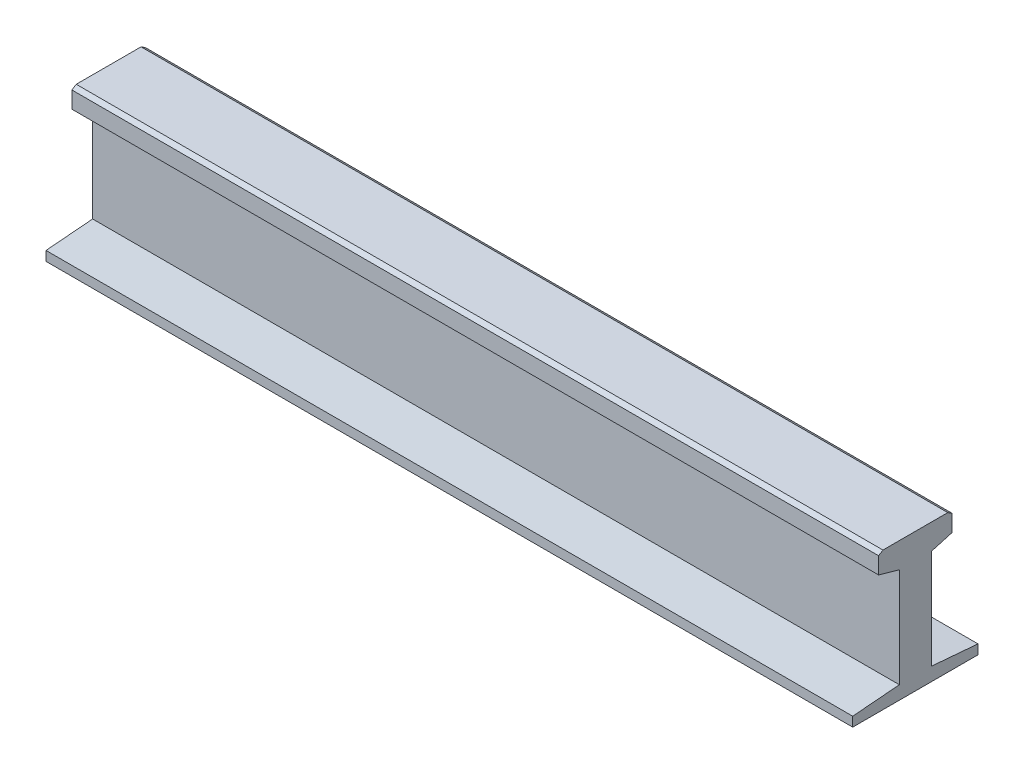
SolidWorks part; units mm, degrees
ref_plane "Спереди" through (0, 0, 0) normal (0, 0, 1) x (1, 0, 0)
ref_plane "Сверху" through (0, 0, 0) normal (0, 1, 0) x (1, 0, 0)
ref_plane "Справа" through (0, 0, 0) normal (1, 0, 0) x (0, 0, -1)
sketch "Эскиз1" plane through (0, 0, 0) normal (1, 0, 0) x (0, 0, -1)
  line L0 (-66, 0) -> (66, 0)
  line L1 (66, 0) -> (66, 10)
  line L2 (66, 10) -> (16.8833, 14.1635)
  line L3 (16.8833, 14.1635) -> (16.8833, 118.9844)
  line L4 (16.8833, 118.9844) -> (38.7045, 125.2191)
  line L5 (-34.151, 145.7096) -> (34.151, 145.7096)
  line L6 (34.151, 145.7096) -> (38.7045, 142.7824)
  line L7 (38.7045, 142.7824) -> (38.7045, 125.2191)
  line L8 (0, 177.3831) -> (0, -45.0863) construction
  line L9 (-38.7045, 142.7824) -> (-38.7045, 125.2191)
  line L10 (-34.151, 145.7096) -> (-38.7045, 142.7824)
  line L11 (-16.8833, 118.9844) -> (-38.7045, 125.2191)
  line L12 (-16.8833, 14.1635) -> (-16.8833, 118.9844)
  line L13 (-66, 10) -> (-16.8833, 14.1635)
  line L14 (-66, 0) -> (-66, 10)
  point P14 (0, 145.7096)
  point P19 (0, 0)
  point P23 (0, 0)
extrude "Бобышка-Вытянуть1" add sketch "Эскиз1" along normal blind 850
